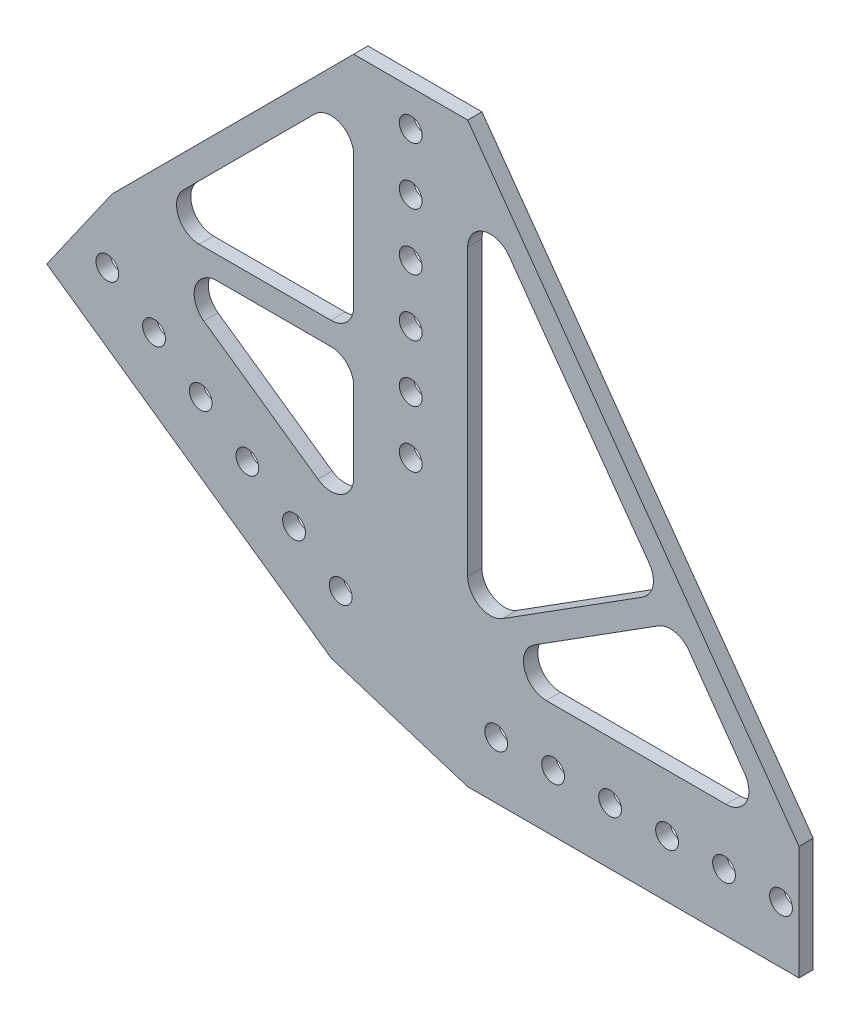
SolidWorks part; units mm, degrees
ref_plane "Front Plane" through (0, 0, 0) normal (0, 0, 1) x (1, 0, 0)
ref_plane "Top Plane" through (0, 0, 0) normal (0, 1, 0) x (1, 0, 0)
ref_plane "Right Plane" through (0, 0, 0) normal (1, 0, 0) x (0, 0, -1)
sketch "Sketch1" plane through (0, 0, 0) normal (0, 0, 1) x (1, 0, 0)
  line L0 (-280.0652, 184.4073) -> (-30.3877, 9.5812)
  line L1 (0, 0) -> (431.8, 0)
  line L2 (0, 0) -> (0, 25.4)
  line L3 (0, 25.4) -> (431.8, 25.4)
  line L4 (431.8, 0) -> (431.8, 25.4)
  line L5 (-280.0652, 184.4073) -> (-265.4964, 205.2137)
  line L6 (-30.3877, 9.5812) -> (-15.8188, 30.3877)
  line L7 (-265.4964, 205.2137) -> (-15.8188, 30.3877)
  line L8 (-25.4, 50.8) -> (0, 50.8)
  line L9 (-25.4, 50.8) -> (-25.4, 355.6)
  line L10 (0, 50.8) -> (0, 355.6)
  line L11 (-25.4, 355.6) -> (0, 355.6)
  line L12 (-225.8432, 161.9445) -> (23.8343, -12.8816) construction
  line L13 (0, 12.7) -> (431.8, 12.7) construction
  line L14 (-12.7, 12.7) -> (-12.7, 105.3379) construction
  line L15 (-12.7, 57.15) -> (-12.7, 69.85) construction
  line L16 (6.35, 12.7) -> (19.05, 12.7) construction
  line L17 (-28.3048, 23.6266) -> (-38.7081, 30.9111) construction
  circle A0 centre (-12.7, 57.15) radius 2.54
  circle A1 centre (-12.7, 69.85) radius 2.54
  circle A2 centre (-12.7, 82.55) radius 2.54
  circle A3 centre (-12.7, 95.25) radius 2.54
  circle A4 centre (-12.7, 107.95) radius 2.54
  circle A5 centre (-12.7, 120.65) radius 2.54
  circle A6 centre (-12.7, 133.35) radius 2.54
  circle A7 centre (-12.7, 146.05) radius 2.54
  circle A8 centre (-12.7, 158.75) radius 2.54
  circle A9 centre (-12.7, 171.45) radius 2.54
  circle A10 centre (-12.7, 184.15) radius 2.54
  circle A11 centre (-12.7, 196.85) radius 2.54
  circle A12 centre (-12.7, 209.55) radius 2.54
  circle A13 centre (-12.7, 222.25) radius 2.54
  circle A14 centre (-12.7, 234.95) radius 2.54
  circle A15 centre (-12.7, 247.65) radius 2.54
  circle A16 centre (-12.7, 260.35) radius 2.54
  circle A17 centre (-12.7, 273.05) radius 2.54
  circle A18 centre (-12.7, 285.75) radius 2.54
  circle A19 centre (-12.7, 298.45) radius 2.54
  circle A20 centre (-12.7, 311.15) radius 2.54
  circle A21 centre (-12.7, 323.85) radius 2.54
  circle A22 centre (-12.7, 336.55) radius 2.54
  circle A23 centre (-12.7, 349.25) radius 2.54
  circle A24 centre (6.35, 12.7) radius 2.54
  circle A25 centre (19.05, 12.7) radius 2.54
  circle A26 centre (31.75, 12.7) radius 2.54
  circle A27 centre (44.45, 12.7) radius 2.54
  circle A28 centre (57.15, 12.7) radius 2.54
  circle A29 centre (69.85, 12.7) radius 2.54
  circle A30 centre (82.55, 12.7) radius 2.54
  circle A31 centre (95.25, 12.7) radius 2.54
  circle A32 centre (107.95, 12.7) radius 2.54
  circle A33 centre (120.65, 12.7) radius 2.54
  circle A34 centre (133.35, 12.7) radius 2.54
  circle A35 centre (146.05, 12.7) radius 2.54
  circle A36 centre (158.75, 12.7) radius 2.54
  circle A37 centre (171.45, 12.7) radius 2.54
  circle A38 centre (184.15, 12.7) radius 2.54
  circle A39 centre (196.85, 12.7) radius 2.54
  circle A40 centre (209.55, 12.7) radius 2.54
  circle A41 centre (222.25, 12.7) radius 2.54
  circle A42 centre (234.95, 12.7) radius 2.54
  circle A43 centre (247.65, 12.7) radius 2.54
  circle A44 centre (260.35, 12.7) radius 2.54
  circle A45 centre (273.05, 12.7) radius 2.54
  circle A46 centre (285.75, 12.7) radius 2.54
  circle A47 centre (298.45, 12.7) radius 2.54
  circle A48 centre (311.15, 12.7) radius 2.54
  circle A49 centre (323.85, 12.7) radius 2.54
  circle A50 centre (336.55, 12.7) radius 2.54
  circle A51 centre (349.25, 12.7) radius 2.54
  circle A52 centre (361.95, 12.7) radius 2.54
  circle A53 centre (374.65, 12.7) radius 2.54
  circle A54 centre (387.35, 12.7) radius 2.54
  circle A55 centre (400.05, 12.7) radius 2.54
  circle A56 centre (412.75, 12.7) radius 2.54
  circle A57 centre (425.45, 12.7) radius 2.54
  circle A58 centre (-28.3048, 23.6266) radius 2.54
  circle A59 centre (-38.7081, 30.9111) radius 2.54
  circle A60 centre (-49.1113, 38.1955) radius 2.54
  circle A61 centre (-59.5145, 45.4799) radius 2.54
  circle A62 centre (-69.9178, 52.7643) radius 2.54
  circle A63 centre (-80.321, 60.0487) radius 2.54
  circle A64 centre (-90.7242, 67.3332) radius 2.54
  circle A65 centre (-101.1275, 74.6176) radius 2.54
  circle A66 centre (-111.5307, 81.902) radius 2.54
  circle A67 centre (-121.9339, 89.1864) radius 2.54
  circle A68 centre (-132.3372, 96.4708) radius 2.54
  circle A69 centre (-142.7404, 103.7553) radius 2.54
  circle A70 centre (-153.1436, 111.0397) radius 2.54
  circle A71 centre (-163.5468, 118.3241) radius 2.54
  circle A72 centre (-173.9501, 125.6085) radius 2.54
  circle A73 centre (-184.3533, 132.8929) radius 2.54
  circle A74 centre (-194.7565, 140.1774) radius 2.54
  circle A75 centre (-205.1598, 147.4618) radius 2.54
  circle A76 centre (-215.563, 154.7462) radius 2.54
  circle A77 centre (-225.9662, 162.0306) radius 2.54
  circle A78 centre (-236.3695, 169.315) radius 2.54
  circle A79 centre (-246.7727, 176.5995) radius 2.54
  circle A80 centre (-257.1759, 183.8839) radius 2.54
  circle A81 centre (-267.5792, 191.1683) radius 2.54
  point P12 (-23.1032, 19.9844)
  point P17 (0, 12.7)
  point P19 (-12.7, 12.7)
  point P22 (-12.7, 50.8)
  dimension "D12" = 5.08
  dimension "D15" = 5.08
  dimension "D19" = 5.08
  dimension "D20" = 6.35
  dimension "D1" = 25.4
  dimension "D2" = 431.8
  dimension "D3" = 25.4
  dimension "D4" = 25.4
  dimension "D5" = 304.8
  dimension "D6" = 304.8
  dimension "D7" = 145
  dimension "D8" = 12.7
  dimension "D9" = 12.7
  dimension "D10" = 38.1
  dimension "D11" = 6.35
  dimension "D14" = 12.7
  dimension "D16" = 6.35
  dimension "D18" = 12.7
  dimension "D21" = 12.7
  dimension "D13" = 24
  dimension "D17" = 34
ref_plane "Plane1" through (0, 0, 0) normal (0, 0, 1) x (1, 0, 0)
sketch "Sketch2" plane through (0, 0, 0) normal (0, 0, 1) x (1, 0, 0)
  line L1 (-59.8216, 74.8099) -> (-30.48, 74.8099)
  line L2 (-55.8936, 69.7299) -> (-30.48, 69.7299)
  line L6 (7.7971, 36.3478) -> (39.0498, 56.1309)
  line L8 (14.8061, 34.7723) -> (42.4769, 52.2881)
  line L12 (-79.2603, 74.8099) -> (-93.8291, 54.0034)
  line L14 (-25.4, 64.6499) -> (-25.4, 46.8551)
  line L17 (-25.4, 128.7126) -> (0, 128.7126)
  line L18 (-25.4, 50.8) -> (-25.4, 355.6) construction
  line L19 (0, 50.8) -> (0, 355.6) construction
  line L20 (0, 128.7126) -> (73.8614, 25.4)
  line L21 (0, 25.4) -> (431.8, 25.4) construction
  line L22 (73.8614, 25.4) -> (73.8614, 0)
  line L23 (0, 0) -> (431.8, 0) construction
  line L24 (73.8614, 0) -> (0, 0)
  line L25 (0, 0) -> (-30.3877, 9.5812)
  line L26 (-30.3877, 9.5812) -> (-93.8291, 54.0034)
  line L27 (-280.0652, 184.4073) -> (-30.3877, 9.5812) construction
  line L29 (-265.4964, 205.2137) -> (-15.8188, 30.3877) construction
  line L30 (-79.2603, 74.8099) -> (-25.4, 128.7126)
  line L31 (-63.4151, 83.4805) -> (-34.0735, 112.8452)
  line L32 (-25.4, 109.2545) -> (-25.4, 79.8899)
  line L33 (-33.3938, 42.6938) -> (-58.8074, 60.4886)
  line L34 (0, 104.1376) -> (0, 40.6401)
  line L35 (17.5231, 25.4) -> (57.6114, 25.4)
  line L36 (40.4652, 63.3777) -> (9.2125, 107.092)
  line L37 (49.3382, 50.9337) -> (61.7556, 33.418)
  arc A0 (57.6114, 25.4) -> (61.7556, 33.418) centre (57.6114, 30.48) ccw
  arc A1 (42.4769, 52.2881) -> (49.3382, 50.9337) centre (45.1939, 47.9958) cw
  arc A2 (14.8061, 34.7723) -> (17.5231, 25.4) centre (17.5231, 30.48) ccw
  arc A3 (7.7971, 36.3478) -> (0, 40.6401) centre (5.08, 40.6401) cw
  arc A4 (39.0498, 56.1309) -> (40.4652, 63.3777) centre (36.3327, 60.4233) ccw
  arc A5 (0, 104.1376) -> (9.2125, 107.092) centre (5.08, 104.1376) cw
  arc A6 (-25.4, 46.8551) -> (-33.3938, 42.6938) centre (-30.48, 46.8551) cw
  arc A7 (-30.48, 69.7299) -> (-25.4, 64.6499) centre (-30.48, 64.6499) cw
  arc A8 (-55.8936, 69.7299) -> (-58.8074, 60.4886) centre (-55.8936, 64.6499) ccw
  arc A9 (-59.8216, 74.8099) -> (-63.4151, 83.4805) centre (-59.8216, 79.8899) cw
  arc A10 (-30.48, 74.8099) -> (-25.4, 79.8899) centre (-30.48, 79.8899) ccw
  arc A11 (-34.0735, 112.8452) -> (-25.4, 109.2545) centre (-30.48, 109.2545) cw
  point P8 (-48.7443, 98.1629)
  point P32 (34.4635, 71.5379)
  point P33 (43.591, 59.0056)
  point P37 (67.4398, 25.4)
  point P40 (46.5501, 54.8665)
  point P43 (0, 25.4)
  point P50 (0, 119.9779)
  point P53 (-25.4, 37.0965)
  point P56 (-25.4, 69.7299)
  point P62 (-72.0053, 69.7299)
  point P69 (-25.4, 121.5256)
  dimension "D1" = 5.08
  dimension "D8" = 5.08
  dimension "D2" = 25.4
  dimension "D3" = 127
  dimension "D4" = 76.2
  dimension "D5" = 5.08
  dimension "D6" = 5.08
  dimension "D7" = 5.08
extrude "Boss-Extrude1" add sketch "Sketch2" along normal blind 3.175
sketch "Sketch3" plane through (0, 0, 0) normal (0, 0, 1) x (1, 0, 0)
  circle A0 centre (-12.7, 57.15) radius 2.54
  circle A1 centre (6.35, 12.7) radius 2.54
  circle A2 centre (-28.3048, 23.6266) radius 2.54
  circle A3 centre (-38.7081, 30.9111) radius 2.54
  circle A4 centre (-49.1113, 38.1955) radius 2.54
  circle A5 centre (-59.5145, 45.4799) radius 2.54
  circle A6 centre (-69.9178, 52.7643) radius 2.54
  circle A7 centre (-80.321, 60.0487) radius 2.54
  circle A8 centre (-12.7, 69.85) radius 2.54
  circle A9 centre (-12.7, 82.55) radius 2.54
  circle A10 centre (-12.7, 95.25) radius 2.54
  circle A11 centre (-12.7, 107.95) radius 2.54
  circle A12 centre (-12.7, 120.65) radius 2.54
  circle A13 centre (19.05, 12.7) radius 2.54
  circle A14 centre (31.75, 12.7) radius 2.54
  circle A15 centre (44.45, 12.7) radius 2.54
  circle A16 centre (57.15, 12.7) radius 2.54
  circle A17 centre (69.85, 12.7) radius 2.54
  dimension "D1" = 6
  dimension "D2" = 6
  dimension "D3" = 6
extrude "Cut-Extrude4" cut sketch "Sketch3" against normal through all and the other way through all
